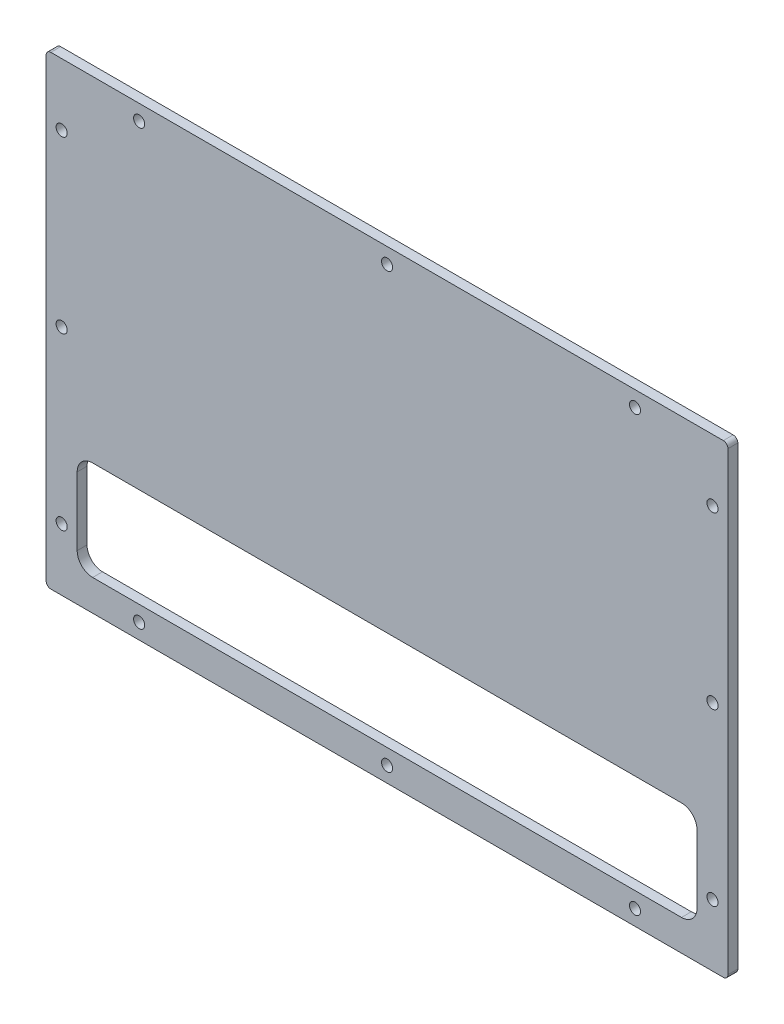
SolidWorks part; units mm, degrees
ref_plane "Front Plane" through (0, 0, 0) normal (0, 0, 1) x (1, 0, 0)
ref_plane "Top Plane" through (0, 0, 0) normal (0, 1, 0) x (1, 0, 0)
ref_plane "Right Plane" through (0, 0, 0) normal (1, 0, 0) x (0, 0, -1)
sketch "Sketch1" plane through (0, 0, 0) normal (0, 0, 1) x (1, 0, 0)
  line L0 (0, 0) -> (0, 75) construction
  line L1 (-110, -75) -> (110, -75)
  line L2 (-110, -75) -> (-110, 75)
  line L3 (-110, 75) -> (110, 75)
  line L4 (110, -75) -> (110, 75)
  line L5 (-110, -75) -> (110, 75) construction
  line L6 (-110, 75) -> (110, -75) construction
  line L15 (0, 0) -> (-110, 0) construction
  point P0 (0, 0)
  dimension "D1" = 220
  dimension "D2" = 150
extrude "Boss-Extrude1" add sketch "Sketch1" along normal blind 3.175
hole_wizard "M3 Clearance Hole1" positions "Sketch2" profile "Sketch3" hole size "M3" standard "ANSI Metric" end condition through all
sketch "Sketch2" plane through (0, 0, 3.175) normal (0, 0, 1) x (1, 0, 0)
  line L1 (-105, -70) -> (105, -70)
  line L2 (-105, -70) -> (-105, 70)
  line L3 (-105, 70) -> (105, 70)
  line L4 (105, -70) -> (105, 70)
  line L5 (-105, -70) -> (105, 70) construction
  line L6 (-105, 70) -> (105, -70) construction
  line L7 (-110, -75) -> (-110, 75) construction
  line L8 (-110, 75) -> (110, 75) construction
  point P2 (0, 0)
  point P113 (-80, 70)
  point P115 (80, 70)
  point P116 (0, 70)
  point P118 (-105, 55)
  point P120 (-105, 0)
  point P122 (-105, -55)
  point P124 (-80, -70)
  point P126 (0, -70)
  point P128 (80, -70)
  point P130 (105, -55)
  point P132 (105, 0)
  point P134 (105, 55)
  dimension "D1" = 5
  dimension "D2" = 5
  dimension "D3" = 80
  dimension "D4" = 80
  dimension "D5" = 55
  dimension "D6" = 55
sketch "Sketch3" plane through (0, 0, 3.175) normal (1, 0, 0) x (0, -1, 0)
  line L0 (0, 0) -> (0, 3.175)
  line L1 (0, 3.175) -> (1.8, 3.175)
  line L2 (1.8, 3.175) -> (1.8, 0)
  line L5 (1.8, 0) -> (0, 0)
  line L11 (0, -6.35) -> (0, 107.95) construction
  dimension "Thru Hole Dia." = 3.6
  dimension "Thru Hole Depth" = 3.175
sketch "Sketch4" plane through (0, 0, 3.175) normal (0, 0, 1) x (1, 0, 0)
  line L1 (-5, -5) -> (5, -5)
  line L2 (-5, -5) -> (-5, 5)
  line L3 (-5, 5) -> (5, 5)
  line L4 (5, -5) -> (5, 5)
  line L5 (-5, -5) -> (5, 5) construction
  line L6 (-5, 5) -> (5, -5) construction
  point P0 (0, 0)
  dimension "D1" = 10
  dimension "D2" = 10
extrude "Boss-Extrude2" add sketch "Sketch4" against normal through all
fillet "Fillet2" radius 1.5 4 edges at (-110, -75, 1.5875) (110, -75, 1.5875) (110, 75, 1.5875) (-110, 75, 1.5875)
sketch "Sketch5" plane through (0, 0, 3.175) normal (0, 0, 1) x (1, 0, 0)
  line L0 (-110, -73.5) -> (-110, 73.5) construction
  line L1 (-100, -65) -> (100, -65)
  line L2 (-100, -65) -> (-100, -33)
  line L3 (-100, -33) -> (100, -33)
  line L4 (100, -65) -> (100, -33)
  line L5 (-100, -65) -> (100, -33) construction
  line L6 (-100, -33) -> (100, -65) construction
  line L7 (-108.5, -75) -> (108.5, -75) construction
  line L8 (110, -73.5) -> (110, 73.5) construction
  point P0 (0, -49)
  dimension "D1" = 10
  dimension "D2" = 10
  dimension "D3" = 10
  dimension "D4" = 32
extrude "Cut-Extrude1" cut sketch "Sketch5" against normal through all
fillet "Fillet3" radius 5 4 edges at (-100, -65, 1.5875) (-100, -33, 1.5875) (100, -65, 1.5875) (100, -33, 1.5875)
